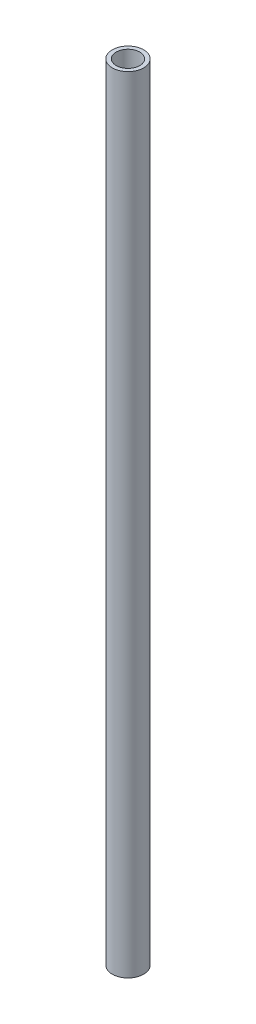
SolidWorks part; units mm, degrees
material "6061 Alloy"
ref_plane "Front Plane" through (0, 0, 0) normal (0, 0, 1) x (1, 0, 0)
ref_plane "Top Plane" through (0, 0, 0) normal (0, 1, 0) x (1, 0, 0)
ref_plane "Right Plane" through (0, 0, 0) normal (1, 0, 0) x (0, 0, -1)
sketch "Sketch1" plane through (0, 0, 0) normal (0, 1, 0) x (1, 0, 0)
  circle A0 centre (0, 0) radius 20
  circle A1 centre (0, 0) radius 15
  dimension "D1" = 40
  dimension "D2" = 5
extrude "Extrude1" add sketch "Sketch1" along normal blind 1000
